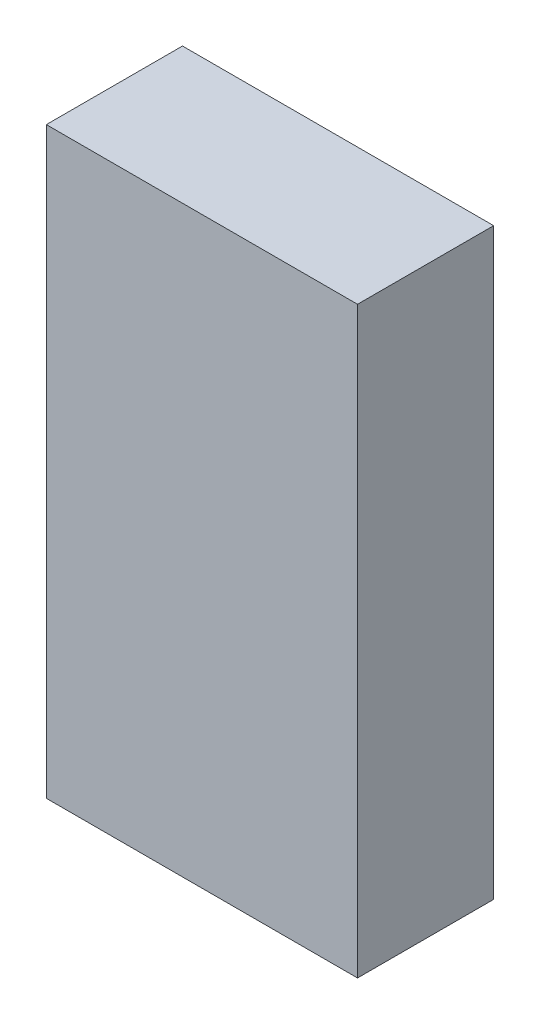
SolidWorks part; units mm, degrees
ref_plane "Front" through (0, 0, 0) normal (0, 0, 1) x (1, 0, 0)
ref_plane "Top" through (0, 0, 0) normal (0, 1, 0) x (1, 0, 0)
ref_plane "Right" through (0, 0, 0) normal (1, 0, 0) x (0, 0, -1)
sketch "草图1" plane through (0, 0, 0) normal (0, 0, 1) x (1, 0, 0)
  line L1 (0, 0) -> (8, 0)
  line L3 (-1.5, 30) -> (8, 30)
  line L4 (8, 0) -> (8, 30)
  line L5 (0, 0) -> (-8, 0)
  line L7 (-1.5, 30) -> (-8, 30)
  line L8 (-8, 0) -> (-8, 30)
  dimension "D1" = 8
  dimension "D2" = 8
  dimension "D3" = 30
extrude "凸台-拉伸1" add sketch "草图1" against normal blind 7
sketch "草图2" plane through (0, 0, 0) normal (0, 0, 1) x (1, 0, 0)
  line L1 (5, 23.5) -> (-5, 23.5)
  line L2 (5, 23.5) -> (5, 11.5)
  line L3 (5, 11.5) -> (-5, 11.5)
  line L4 (-5, 23.5) -> (-5, 11.5)
  point P4 (-5, 17.5)
  point P6 (0, 11.5)
  dimension "D1" = 17.5
  dimension "D3" = 10
  dimension "D2" = 0
  dimension "D4" = 12
